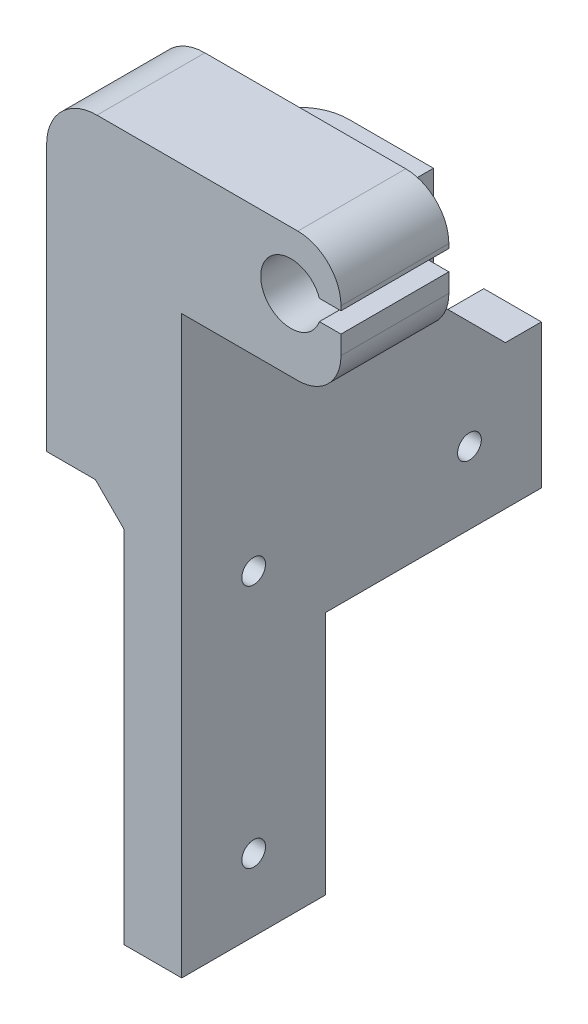
SolidWorks part; units mm, degrees
ref_plane "前视基准面" through (0, 0, 0) normal (0, 0, 1) x (1, 0, 0)
ref_plane "上视基准面" through (0, 0, 0) normal (0, 1, 0) x (1, 0, 0)
ref_plane "右视基准面" through (0, 0, 0) normal (1, 0, 0) x (0, 0, -1)
sketch "草图1" plane through (0, 0, 0) normal (0, 0, 1) x (1, 0, 0)
  line L0 (8, 26) -> (27.14, 26)
  line L1 (8, -54) -> (8, 26)
  line L2 (27.14, 26) -> (27.14, 44)
  line L3 (27.14, 44) -> (-10.78, 44)
  line L4 (-10.78, 44) -> (-10.78, 0)
  line L5 (-10.78, 0) -> (0, 0)
  line L6 (0, 0) -> (0, -54)
  line L8 (8, -54) -> (0, -54)
extrude "凸台-拉伸1" add sketch "草图1" along normal blind 15
sketch "草图4" plane through (0, 0, 0) normal (0, 0, -1) x (-1, 0, 0)
  line L0 (-8, 26) -> (10.78, 26)
  line L1 (10.78, 44) -> (10.78, 0) construction
  line L2 (10.78, 26) -> (10.78, 0)
  line L3 (10.78, 0) -> (-8, 0)
  line L4 (-8, -54) -> (-8, 26) construction
  line L5 (-8, 0) -> (-8, 26)
extrude "凸台-拉伸4" add sketch "草图4" along normal blind 20
sketch "草图5" plane through (0, 0, 0) normal (0, 0, -1) x (-1, 0, 0)
  line L1 (-8, 0) -> (0, 0)
  line L2 (-8, 0) -> (-8, -54)
  line L3 (-8, -54) -> (0, -54)
  line L4 (0, 0) -> (0, -54)
extrude "凸台-拉伸5" add sketch "草图5" along normal blind 5
sketch "草图6" plane through (0, 0, 0) normal (0, 0, -1) x (-1, 0, 0)
  circle A1 centre (-23.18, 36) radius 4.2
extrude "切除-拉伸1" cut sketch "草图6" against normal blind 15
chamfer "倒角1" distance 4 angle 45 1 edges
fillet "圆角3" radius 7 1 edges at (-10.78, 44, 7.5)
fillet "圆角4" radius 7 1 edges at (-10.78, 13, -20)
sketch "草图9" plane through (0, 0, -5) normal (0, 0, -1) x (-1, 0, 0)
  line L0 (0, -54) -> (0, -4) construction
  line L1 (-8, 0) -> (0, 0)
  line L2 (-8, 0) -> (-8, -20)
  line L3 (-8, -20) -> (0, -20)
  line L4 (0, 0) -> (0, -20)
extrude "凸台-拉伸6" add sketch "草图9" along normal blind 30
sketch "草图10" plane through (0, 0, 0) normal (-1, 0, 0) x (0, 0, 1)
  circle A0 centre (-25, -10) radius 1.65
  circle A1 centre (5, -10) radius 1.65
  circle A2 centre (5, -44) radius 1.65
extrude "切除-拉伸4" cut sketch "草图10" against normal blind 30
chamfer "倒角2" distance 10 angle 45 1 edges at (4, 0, -20)
sketch "草图11" plane through (0, 0, 15) normal (0, 0, 1) x (1, 0, 0)
  line L0 (27.14, 44) -> (30.14, 44)
  line L1 (27.14, 44) -> (27.14, 37.3994)
  line L2 (27.14, 37.3994) -> (30.14, 37.3994)
  line L3 (30.14, 37.3994) -> (30.14, 44)
  line L4 (27.14, 34.6006) -> (30.14, 34.6006)
  line L5 (30.14, 34.6006) -> (30.14, 26)
  line L6 (27.14, 34.6006) -> (27.14, 26)
  line L7 (27.14, 26) -> (30.14, 26)
extrude "凸台-拉伸7" add sketch "草图11" against normal blind 15
fillet "圆角5" radius 6 1 edges at (30.14, 44, 7.5)
sketch "草图8" plane through (0, 26, 0) normal (0, 1, 0) x (1, 0, 0)
  circle A1 centre (1.22, 10.05) radius 1.6
extrude "切除-拉伸3" cut sketch "草图8" against normal blind 93
fillet "圆角6" radius 6 1 edges at (30.14, 26, 7.5)
